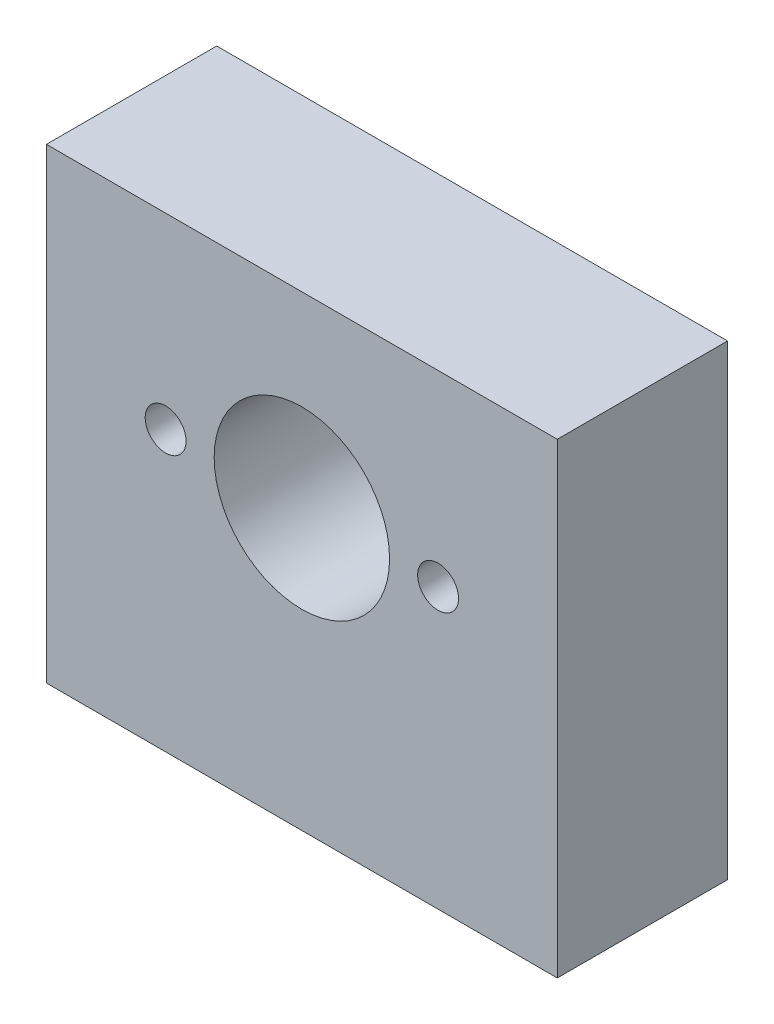
SolidWorks part; units mm, degrees
ref_plane "Front Plane" through (0, 0, 0) normal (0, 0, 1) x (1, 0, 0)
ref_plane "Top Plane" through (0, 0, 0) normal (0, 1, 0) x (1, 0, 0)
ref_plane "Right Plane" through (0, 0, 0) normal (1, 0, 0) x (0, 0, -1)
sketch "Sketch1" plane through (0, 0, 0) normal (0, 0, 1) x (1, 0, 0)
  line L1 (15, -16.4) -> (-15, -16.4)
  line L2 (15, -16.4) -> (15, 11)
  line L3 (15, 11) -> (-15, 11)
  line L4 (-15, -16.4) -> (-15, 11)
  circle A0 centre (0, 0) radius 11 construction
  circle A1 centre (0, 0) radius 5.15
  point P0 (0, 0)
  point P8 (0, 0)
  point P9 (-15, -2.7)
  point P10 (0, 11)
  dimension "D1" = 22
  dimension "D4" = 10.3
  dimension "D2" = 16.4
  dimension "D3" = 30
extrude "Boss-Extrude1" add sketch "Sketch1" along normal blind 10
sketch "Sketch2" plane through (0, -16.4, 0) normal (0, -1, 0) x (1, 0, 0)
  line L0 (0, 10) -> (0, 0) construction
  line L1 (-15, 10) -> (15, 10) construction
  circle A0 centre (-11, 5) radius 2
  circle A1 centre (11, 5) radius 2
  point P10 (0, 5)
  dimension "D2" = 4
  dimension "D1" = 22
extrude "Cut-Extrude1" cut sketch "Sketch2" against normal blind 10
sketch "Sketch7" plane through (0, 0, 10) normal (0, 0, 1) x (1, 0, 0)
  line L0 (0, 11) -> (0, 0) construction
  line L1 (15, 11) -> (-15, 11) construction
  circle A0 centre (-8, 0) radius 1.2
  circle A1 centre (8, 0) radius 1.2
  dimension "D1" = 2.4
  dimension "D2" = 16
extrude "Cut-Extrude2" cut sketch "Sketch7" against normal through all
